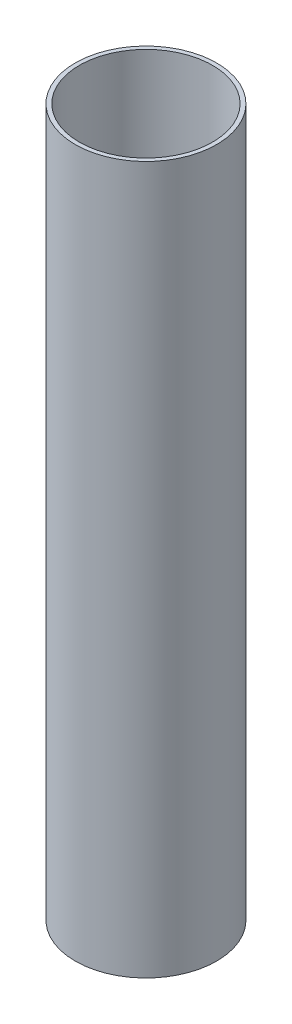
SolidWorks part; units mm, degrees
ref_plane "Front Plane" through (0, 0, 0) normal (0, 0, 1) x (1, 0, 0)
ref_plane "Top Plane" through (0, 0, 0) normal (0, 1, 0) x (1, 0, 0)
ref_plane "Right Plane" through (0, 0, 0) normal (1, 0, 0) x (0, 0, -1)
sketch "Sketch1" plane through (0, 0, 0) normal (0, 1, 0) x (1, 0, 0)
  circle A0 centre (0, 0) radius 6.35
  circle A1 centre (0, 0) radius 5.9805
  dimension "D1" = 12.7
  dimension "D2" = 11.961
sketch "Sketch2" plane through (0, 0, 0) normal (1, 0, 0) x (0, 0, -1)
  line L0 (0, 0) -> (0, 63.5)
  dimension "D1" = 63.5
sweep "Sweep1" add profiles "Sketch1" path "Sketch2"
